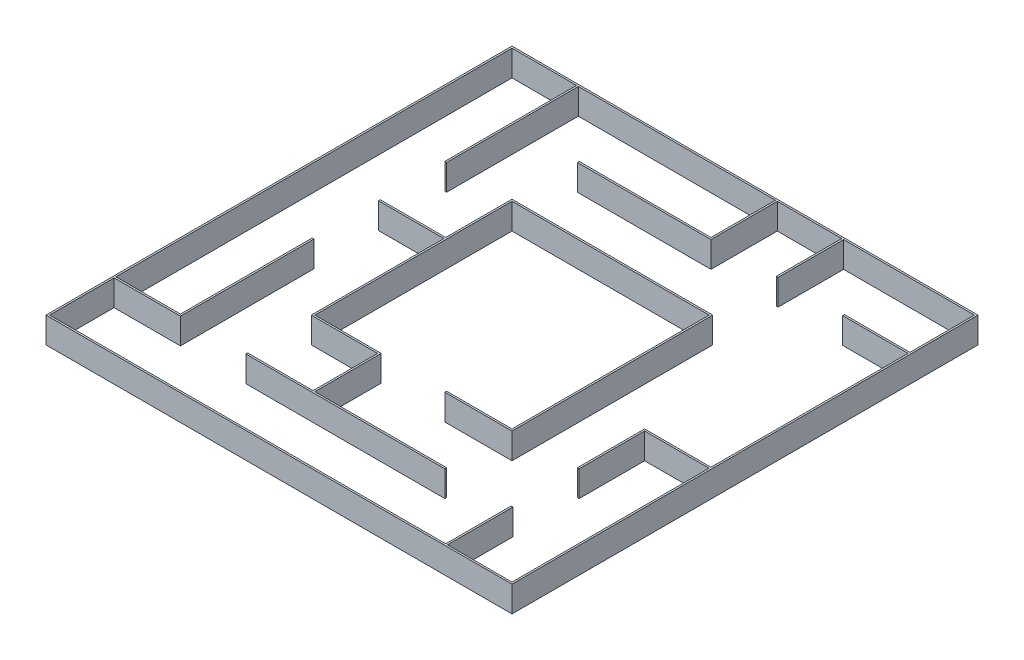
SolidWorks part; units mm, degrees
ref_plane "Front Plane" through (0, 0, 0) normal (0, 0, 1) x (1, 0, 0)
ref_plane "Top Plane" through (0, 0, 0) normal (0, 1, 0) x (1, 0, 0)
ref_plane "Right Plane" through (0, 0, 0) normal (1, 0, 0) x (0, 0, -1)
ref_plane "Plane1" through (0, 48.2717, 0) normal (0, 1, 0) x (1, 0, 0)
sketch "Sketch1" plane through (0, 48.2717, 0) normal (0, 1, 0) x (1, 0, 0)
  line L0 (-1322.6892, -1330.1316) -> (1277.3108, -1330.1316)
  line L1 (1277.3108, -1330.1316) -> (1277.3108, 1269.8684)
  line L2 (1277.3108, 1269.8684) -> (-1322.6892, 1269.8684)
  line L3 (-1322.6892, 1269.8684) -> (-1322.6892, -1330.1316)
extrude "Boss-Extrude1" add sketch "Sketch1" against normal blind 150
sketch "Sketch2" plane through (0, 48.2717, 0) normal (0, 1, 0) x (-1, 0, 0)
  line L0 (-902.3108, -899.8684) -> (-907.3108, -899.8684)
  line L1 (-907.3108, -899.8684) -> (-907.3108, -1259.8684)
  line L2 (-907.3108, -1259.8684) -> (-537.3108, -1259.8684)
  line L3 (-537.3108, -1259.8684) -> (-537.3108, -894.8684)
  line L4 (-537.3108, -894.8684) -> (-527.3108, -894.8684)
  line L5 (-527.3108, -894.8684) -> (-527.3108, -1259.8684)
  line L6 (-527.3108, -1259.8684) -> (-167.3108, -1259.8684)
  line L7 (-167.3108, -1259.8684) -> (-167.3108, -889.8684)
  line L8 (-167.3108, -889.8684) -> (577.6892, -889.8684)
  line L9 (577.6892, -889.8684) -> (577.6892, -899.8684)
  line L10 (577.6892, -899.8684) -> (-157.3108, -899.8684)
  line L11 (-157.3108, -899.8684) -> (-157.3108, -1259.8684)
  line L12 (-157.3108, -1259.8684) -> (942.6892, -1259.8684)
  line L13 (942.6892, -1259.8684) -> (942.6892, -524.8684)
  line L14 (942.6892, -524.8684) -> (952.6892, -524.8684)
  line L15 (952.6892, -524.8684) -> (952.6892, -899.8684)
  line L16 (952.6892, -899.8684) -> (1312.6892, -899.8684)
  line L17 (1312.6892, -899.8684) -> (1312.6892, 950.1316)
  line L18 (1312.6892, 950.1316) -> (952.6892, 950.1316)
  line L19 (952.6892, 950.1316) -> (952.6892, 215.1316)
  line L20 (952.6892, 215.1316) -> (942.6892, 215.1316)
  line L21 (942.6892, 215.1316) -> (942.6892, 960.1316)
  line L22 (942.6892, 960.1316) -> (952.6892, 960.1316)
  line L23 (952.6892, 960.1316) -> (952.6892, 1320.1316)
  line L24 (952.6892, 1320.1316) -> (-897.3108, 1320.1316)
  line L25 (-897.3108, 1320.1316) -> (-897.3108, 955.1316)
  line L26 (-897.3108, 955.1316) -> (-907.3108, 955.1316)
  line L27 (-907.3108, 955.1316) -> (-907.3108, 960.1316)
  line L28 (-907.3108, 960.1316) -> (-1267.3108, 960.1316)
  line L29 (-1267.3108, 960.1316) -> (-1267.3108, 220.1316)
  line L30 (-1267.3108, 220.1316) -> (-907.3108, 220.1316)
  line L31 (-907.3108, 220.1316) -> (-907.3108, 585.1316)
  line L32 (-907.3108, 585.1316) -> (-897.3108, 585.1316)
  line L33 (-897.3108, 585.1316) -> (-897.3108, 210.1316)
  line L34 (-897.3108, 210.1316) -> (-1267.3108, 210.1316)
  line L35 (-1267.3108, 210.1316) -> (-1267.3108, -889.8684)
  line L36 (-1267.3108, -889.8684) -> (-902.3108, -889.8684)
  line L37 (-902.3108, -889.8684) -> (-902.3108, -899.8684)
extrude "Cut-Extrude1" cut sketch "Sketch2" against normal blind 147
sketch "Sketch3" plane through (0, -98.7283, 0) normal (0, 1, 0) x (-1, 0, 0)
  line L0 (572.6892, 580.1316) -> (202.6892, 580.1316)
  line L1 (202.6892, 580.1316) -> (202.6892, 950.1316)
  line L2 (202.6892, 950.1316) -> (-532.3108, 950.1316)
  line L3 (-532.3108, 950.1316) -> (-532.3108, 960.1316)
  line L4 (-532.3108, 960.1316) -> (577.6892, 960.1316)
  line L5 (577.6892, 960.1316) -> (577.6892, 950.1316)
  line L6 (577.6892, 950.1316) -> (212.6892, 950.1316)
  line L7 (212.6892, 950.1316) -> (212.6892, 590.1316)
  line L8 (212.6892, 590.1316) -> (582.6892, 590.1316)
  line L9 (582.6892, 590.1316) -> (582.6892, -149.8684)
  line L10 (582.6892, -149.8684) -> (947.6892, -149.8684)
  line L11 (947.6892, -149.8684) -> (947.6892, -159.8684)
  line L12 (947.6892, -159.8684) -> (582.6892, -159.8684)
  line L13 (582.6892, -159.8684) -> (582.6892, -529.8684)
  line L14 (582.6892, -529.8684) -> (-537.3108, -529.8684)
  line L15 (-537.3108, -529.8684) -> (-537.3108, 590.1316)
  line L16 (-537.3108, 590.1316) -> (-162.3108, 590.1316)
  line L17 (-162.3108, 590.1316) -> (-162.3108, 580.1316)
  line L18 (-162.3108, 580.1316) -> (-527.3108, 580.1316)
  line L19 (-527.3108, 580.1316) -> (-527.3108, -149.8684)
  line L20 (-527.3108, -149.8684) -> (572.6892, -149.8684)
  line L21 (572.6892, -149.8684) -> (572.6892, 580.1316)
extrude "Boss-Extrude2" add sketch "Sketch3" along normal blind 147
ref_plane "Plane2" through (0, 0, -519.8684) normal (0, 0, -1) x (-1, 0, 0)
sketch "Sketch4" plane through (0, 0, -519.8684) normal (0, 0, -1) x (-1, 0, 0)
  line L0 (572.6892, -95.7283) -> (572.6892, 48.2717)
  line L1 (572.6892, 48.2717) -> (-527.3108, 48.2717)
  line L2 (-527.3108, 48.2717) -> (-527.3108, -95.7283)
  line L3 (-527.3108, -95.7283) -> (572.6892, -95.7283)
extrude "Cut-Extrude2" cut sketch "Sketch4" against normal up to next
sketch "Sketch5" plane through (0, -95.7283, 0) normal (0, 1, 0) x (-1, 0, 0)
  line L0 (572.6892, -159.8684) -> (212.6892, -159.8684)
  line L1 (212.6892, -159.8684) -> (212.6892, -519.8684)
  line L2 (212.6892, -519.8684) -> (572.6892, -519.8684)
  line L3 (572.6892, -519.8684) -> (572.6892, -159.8684)
extrude "Cut-Extrude3" cut sketch "Sketch5" against normal blind 3
sketch "Sketch6" plane through (0, -95.7283, 0) normal (0, 1, 0) x (-1, 0, 0)
  line L0 (-167.3108, -159.8684) -> (-527.3108, -159.8684)
  line L1 (-527.3108, -159.8684) -> (-527.3108, -519.8684)
  line L2 (-527.3108, -519.8684) -> (-167.3108, -519.8684)
  line L3 (-167.3108, -519.8684) -> (-167.3108, -159.8684)
extrude "Cut-Extrude4" cut sketch "Sketch6" against normal blind 3
sketch "Sketch7" plane through (0, -95.7283, 0) normal (0, 1, 0) x (-1, 0, 0)
  line L0 (202.6892, -159.8684) -> (-157.3108, -159.8684)
  line L1 (-157.3108, -159.8684) -> (-157.3108, -519.8684)
  line L2 (-157.3108, -519.8684) -> (202.6892, -519.8684)
  line L3 (202.6892, -519.8684) -> (202.6892, -159.8684)
extrude "Cut-Extrude5" cut sketch "Sketch7" against normal blind 3
ref_plane "Plane3" through (0, -95.7283, 0) normal (0, -1, 0) x (1, 0, 0)
sketch "Sketch9" plane through (0, -95.7283, 0) normal (0, -1, 0) x (1, 0, 0)
  line L0 (1267.3108, -1259.8684) -> (1267.3108, -899.8684)
  line L1 (1267.3108, -899.8684) -> (907.3108, -899.8684)
  line L2 (907.3108, -899.8684) -> (907.3108, -1259.8684)
  line L3 (907.3108, -1259.8684) -> (1267.3108, -1259.8684)
extrude "Cut-Extrude6" cut sketch "Sketch9" against normal up to surface up to plane "Plane1"
sketch "Sketch11" plane through (0, -95.7283, 0) normal (0, -1, 0) x (1, 0, 0)
  line L0 (1267.3108, 960.1316) -> (1267.3108, 1320.1316)
  line L1 (1267.3108, 1320.1316) -> (907.3108, 1320.1316)
  line L2 (907.3108, 1320.1316) -> (907.3108, 960.1316)
  line L3 (907.3108, 960.1316) -> (1267.3108, 960.1316)
extrude "Cut-Extrude7" cut sketch "Sketch11" against normal up to surface up to plane "Plane1"
sketch "Sketch13" plane through (0, -95.7283, 0) normal (0, -1, 0) x (1, 0, 0)
  line L0 (-1312.6892, 1320.1316) -> (-1312.6892, 960.1316)
  line L1 (-1312.6892, 960.1316) -> (-952.6892, 960.1316)
  line L2 (-952.6892, 960.1316) -> (-952.6892, 1320.1316)
  line L3 (-952.6892, 1320.1316) -> (-1312.6892, 1320.1316)
extrude "Cut-Extrude8" cut sketch "Sketch13" against normal up to surface up to plane "Plane1"
sketch "Sketch15" plane through (0, -95.7283, 0) normal (0, -1, 0) x (1, 0, 0)
  line L0 (-1312.6892, -899.8684) -> (-1312.6892, -1259.8684)
  line L1 (-1312.6892, -1259.8684) -> (-952.6892, -1259.8684)
  line L2 (-952.6892, -1259.8684) -> (-952.6892, -899.8684)
  line L3 (-952.6892, -899.8684) -> (-1312.6892, -899.8684)
extrude "Cut-Extrude9" cut sketch "Sketch15" against normal up to surface up to plane "Plane1"
sketch "Sketch18" plane through (0, -101.7283, 0) normal (0, -1, 0) x (1, 0, 0)
  line L1 (-1322.6892, 1330.1316) -> (1277.3108, 1330.1316)
  line L2 (-1322.6892, 1330.1316) -> (-1322.6892, -1269.8684)
  line L3 (-1322.6892, -1269.8684) -> (1277.3108, -1269.8684)
  line L4 (1277.3108, 1330.1316) -> (1277.3108, -1269.8684)
  line L5 (-1322.6892, 1330.1316) -> (1277.3108, -1269.8684) construction
  line L6 (-1322.6892, -1269.8684) -> (1277.3108, 1330.1316) construction
  point P4 (-22.6892, 30.1316)
extrude "Cut-Extrude10" cut sketch "Sketch18" against normal up to surface (6 mm away) up to face at (1087.3108, -95.7283, 1140.1316)
